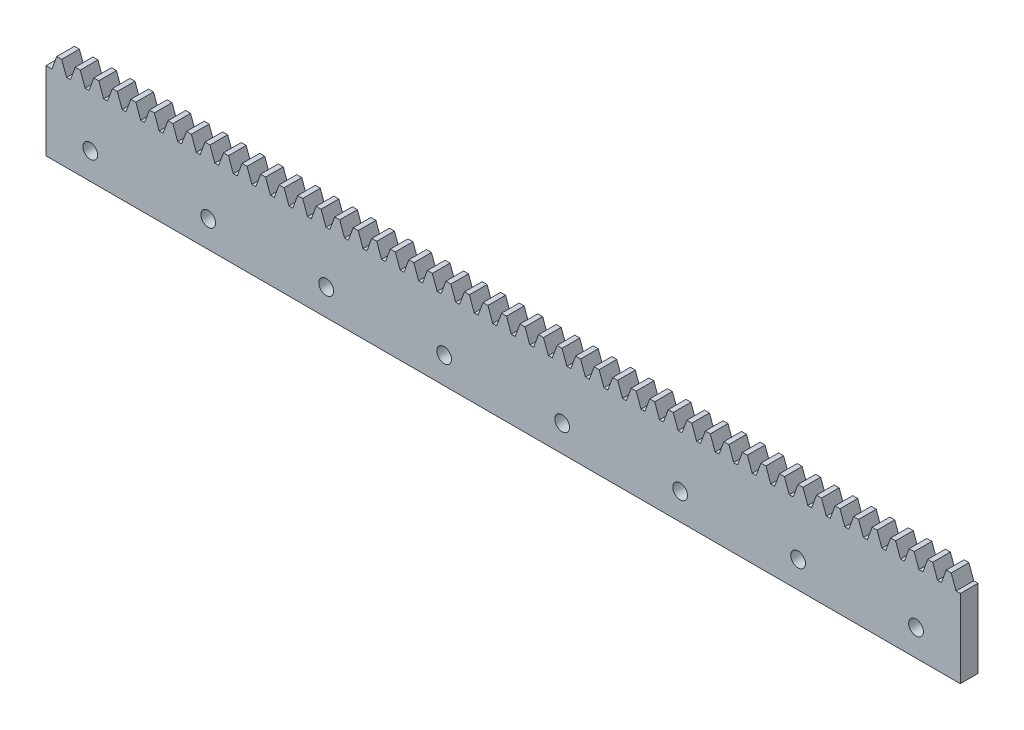
SolidWorks part; units mm, degrees
material "AISI 304"
ref_plane "前基準面" through (0, 0, 0) normal (0, 0, 1) x (1, 0, 0)
ref_plane "上基準面" through (0, 0, 0) normal (0, 1, 0) x (1, 0, 0)
ref_plane "右基準面" through (0, 0, 0) normal (1, 0, 0) x (0, 0, -1)
sketch "草圖1" plane through (0, 0, 0) normal (0, 0, 1) x (1, 0, 0)
  line L1 (-77.5, -4.5) -> (77.5, -4.5)
  line L2 (-77.5, -4.5) -> (-77.5, 4.5)
  line L3 (-77.5, 4.5) -> (77.5, 4.5)
  line L4 (77.5, -4.5) -> (77.5, 4.5)
  line L5 (-77.5, -4.5) -> (77.5, 4.5) construction
  line L6 (-77.5, 4.5) -> (77.5, -4.5) construction
  point P0 (0, 0)
  dimension "D1" = 155
  dimension "D2" = 9
extrude "填料-伸長1" add sketch "草圖1" along normal blind 3
sketch "草圖3" plane through (0, 4.5, 0) normal (0, 1, 0) x (1, 0, 0)
  line L4 (77.5, 0) -> (-77.5, 0)
  line L5 (-77.5, 0) -> (-77.5, -3)
  line L6 (-77.5, -3) -> (77.5, -3)
  line L7 (77.5, -3) -> (77.5, 0)
  line L8 (77.5, 0) -> (-77.5, 0)
  line L9 (-77.5, 0) -> (-77.5, -3)
  line L10 (-77.5, -3) -> (77.5, -3)
  line L11 (77.5, -3) -> (77.5, 0)
  dimension "D1" = 0
extrude "填料-伸長2" add sketch "草圖3" along normal blind 4.25
sketch "草圖4" plane through (0, 0, 0) normal (0, 0, 1) x (1, 0, 0)
  line L0 (-76.5, 8.75) -> (-74.0193, 8.75)
  line L1 (-77.5, 8.75) -> (77.5, 8.75) construction
  line L2 (-74.0193, 8.75) -> (-74.8382, 11)
  line L3 (-74.8382, 11) -> (-75.6811, 11)
  line L4 (-75.6811, 11) -> (-76.5, 8.75)
  line L5 (-76.045, 10) -> (-74.4742, 10) construction
  dimension "D1" = 2.25
  dimension "D2" = 1
  dimension "D3" = 40
  dimension "D4" = 1
  dimension "D5" = 1.5708
extrude "填料-伸長3" add sketch "草圖4" along normal through all
hole_wizard "M3x0.5 螺紋孔1" positions "草圖5" profile "草圖6" tap size "M3x0.5" standard "Ansi Metric" end condition through all
sketch "草圖5" plane through (0, 0, 3) normal (0, 0, 1) x (1, 0, 0)
  line L0 (0, 0) -> (-70, 0) construction
  line L1 (-77.5, 8.75) -> (-77.5, -4.5) construction
  point P2 (-70, 0)
  dimension "D1" = 7.5
sketch "草圖6" plane through (-70, 0, 3) normal (1, 0, 0) x (0, -1, 0)
  line L0 (0, 0) -> (0, 3)
  line L1 (0, 3) -> (1.25, 3)
  line L2 (1.25, 3) -> (1.25, 0)
  line L5 (1.25, 0) -> (0, 0)
  line L11 (0, -6.35) -> (0, 107.95) construction
  dimension "貫穿螺孔鑽直徑" = 2.5
  dimension "貫穿螺孔鑽深度" = 3
pattern_linear "直線複製排列1" count 49 spacing 3.1416 along (1, 0, 0) of "填料-伸長3"
pattern_linear "直線複製排列2" count 8 spacing 20 along (1, 0, 0) of "M3x0.5 螺紋孔1"
equation "\"M\"= 1"
equation "\"D1@草圖4\"=\"M\"*2.25"
equation "\"D2@草圖4\"=\"M\"*1"
equation "\"D5@草圖4\"=\"M\"*PI/2"
equation "\"D3@直線複製排列1\"=\"M\"*PI"
